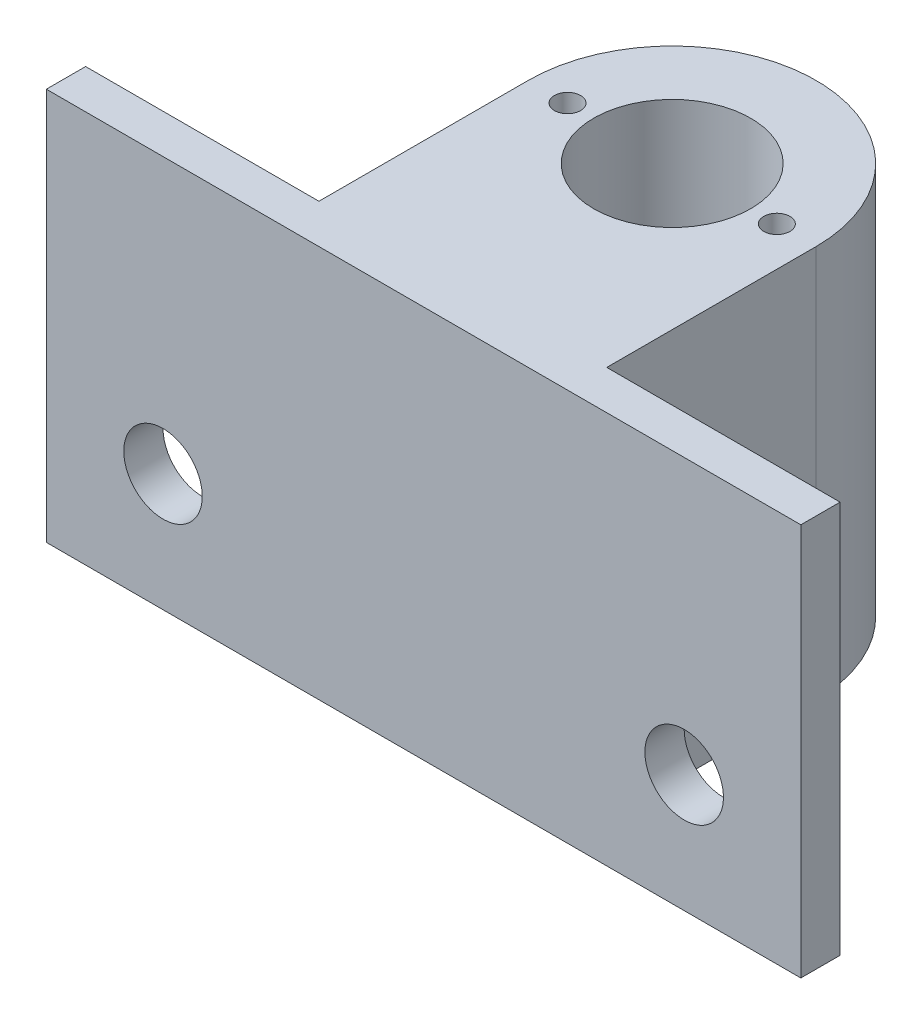
SolidWorks part; units mm, degrees
ref_plane "Front Plane" through (0, 0, 0) normal (0, 0, 1) x (1, 0, 0)
ref_plane "Top Plane" through (0, 0, 0) normal (0, 1, 0) x (1, 0, 0)
ref_plane "Right Plane" through (0, 0, 0) normal (1, 0, 0) x (0, 0, -1)
sketch "Sketch1" plane through (0, 0, 0) normal (0, 1, 0) x (1, 0, 0)
  line L1 (-28.8339, 15) -> (28.8339, 15)
  line L2 (-28.8339, 15) -> (-28.8339, -15)
  line L3 (-28.8339, -15) -> (28.8339, -15)
  line L4 (28.8339, 15) -> (28.8339, -15)
  line L5 (-28.8339, 15) -> (28.8339, -15) construction
  line L6 (-28.8339, -15) -> (28.8339, 15) construction
  point P0 (0, 0)
  dimension "D1" = 30
extrude "Boss-Extrude1" add sketch "Sketch1" along normal blind 30
sketch "Sketch2" plane through (0, 30, 0) normal (0, 1, 0) x (1, 0, 0)
  circle A0 centre (0, 4) radius 6
  dimension "D1" = 12
extrude "Cut-Extrude2" cut sketch "Sketch2" against normal blind 40
sketch "Sketch4" plane through (0, 30, 0) normal (0, 1, 0) x (1, 0, 0)
  line L0 (11, 4) -> (11, -12)
  line L1 (11, -12) -> (28.8339, -12)
  line L2 (28.8339, -15) -> (28.8339, 15) construction
  line L3 (28.8339, -12) -> (28.8339, -15)
  line L4 (28.8339, -15) -> (-28.8339, -15)
  line L5 (-28.8339, -15) -> (-28.8339, -12)
  line L6 (-28.8339, 15) -> (-28.8339, -15) construction
  line L7 (-28.8339, -12) -> (-11, -12)
  line L8 (-11, -12) -> (-11, 4)
  line L9 (-28.8339, -12) -> (-28.8339, 15)
  line L10 (-28.8339, 15) -> (28.8339, 15)
  line L11 (28.8339, 15) -> (28.8339, -12)
  line L12 (-7.5498, -4) -> (-7.5498, -12)
  line L13 (-7.5498, -12) -> (7.5498, -12)
  line L14 (7.5498, -12) -> (7.5498, -4)
  circle A0 centre (0, 4) radius 11
  line M6 (28.8339, -15) -> (28.8339, 15)
  line M7 (28.8339, 15) -> (-28.8339, 15)
  line M8 (-28.8339, 15) -> (-28.8339, -15)
  dimension "D5" = 22
  dimension "D1" = 3
  dimension "D2" = 3
  dimension "D3" = 8
  dimension "D4" = 8
extrude "Cut-Extrude3" cut sketch "Sketch4" against normal through all contours A0 L0 L1 M6 M7 | A0 L10 L7 L8 M8
sketch "Sketch8" plane through (0, 30, 0) normal (0, 1, 0) x (1, 0, 0)
  circle A0 centre (-8, 4) radius 1
  circle A1 centre (8, 4) radius 1
  dimension "D1" = 2
  dimension "D2" = 2
extrude "Cut-Extrude6" cut sketch "Sketch8" against normal blind 10
sketch "Sketch10" plane through (0, 0, 12) normal (0, 0, -1) x (-1, 0, 0)
  line L0 (-11, 0) -> (-28.8339, 0) construction
  line L1 (28.8339, 0) -> (11, 0) construction
  circle A0 centre (19.917, 9) radius 3
  circle A1 centre (-19.917, 9) radius 3
  dimension "D1" = 6
  dimension "D2" = 6
  dimension "D3" = 9
  dimension "D4" = 9
extrude "Cut-Extrude8" cut sketch "Sketch10" against normal blind 10
